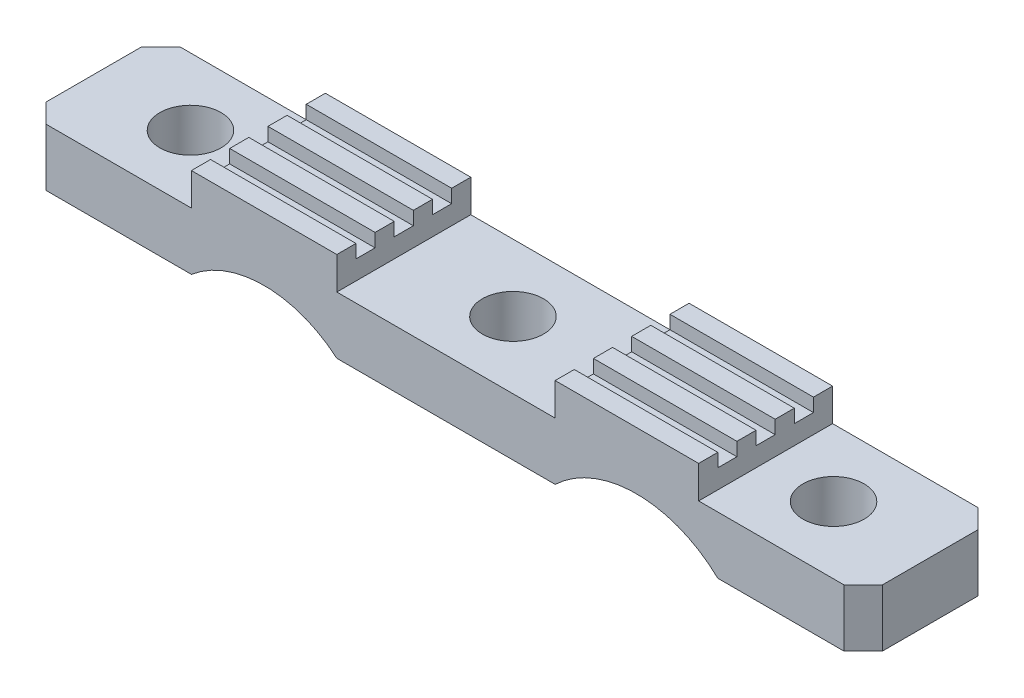
SolidWorks part; units mm, degrees
ref_plane "Front Plane" through (0, 0, 0) normal (0, 0, 1) x (1, 0, 0)
ref_plane "Top Plane" through (0, 0, 0) normal (0, 1, 0) x (1, 0, 0)
ref_plane "Right Plane" through (0, 0, 0) normal (1, 0, 0) x (0, 0, -1)
sketch "Sketch1" plane through (0, 0, 0) normal (0, 0, 1) x (1, 0, 0)
  line L0 (17.11, -3) -> (8.41, -3)
  line L1 (8.41, -3) -> (8.41, -5)
  line L2 (8.41, -5) -> (-2.8, -5)
  line L3 (-11.6, -5) -> (-11.5, -5)
  line L4 (17.11, -3) -> (17.11, -5)
  line L5 (17.11, -5) -> (22.11, -5)
  line L7 (-2.8, -5) -> (-2.8, -3)
  line L8 (-2.8, -3) -> (-11.6, -3)
  line L9 (-11.6, -3) -> (-11.6, -5)
  line L10 (-11.6, -5) -> (-16.6, -5)
  line L12 (-16.6, -5) -> (-16.6, -8)
  line L13 (-16.6, -8) -> (22.11, -8)
  line L14 (22.11, -8) -> (22.11, -5)
  line L15 (-11.5, -5) -> (-11.5, -3)
  line L16 (-2.8, -5) -> (-2.9, -5)
  line L17 (-2.9, -5) -> (-2.9, -3)
  line L18 (8.41, -5) -> (8.51, -5)
  line L19 (8.51, -5) -> (8.51, -3)
  line L20 (17.11, -5) -> (17.01, -5)
  line L21 (17.01, -5) -> (17.01, -3)
  point P7 (-16.6, -9.4349)
  dimension "D1" = 3
  dimension "D2" = 5
  dimension "D3" = 5
  dimension "D4" = 0.1
  dimension "D5" = 0.1
  dimension "D6" = 0.1
  dimension "D7" = 0.1
  dimension "D8" = 38.71
  dimension "D9" = 3
  dimension "D10" = 2
  dimension "D11" = 2
extrude "Boss-Extrude1" add sketch "Sketch1" against normal blind 7
sketch "Sketch2" plane through (-11.5, 0, 0) normal (-1, 0, 0) x (0, 0, 1)
  line L16 (0, -3) -> (-1, -3)
  line L17 (-7, -3) -> (0, -3) construction
  line L18 (-1, -3) -> (-1, -4)
  line L19 (-1, -4) -> (-2, -4)
  line L20 (-2, -4) -> (-2, -3)
  line L21 (-2, -3) -> (-3, -3)
  line L22 (-3, -3) -> (-3, -4)
  line L23 (-3, -4) -> (-4, -4)
  line L24 (-4, -4) -> (-4, -3)
  line L25 (-4, -3) -> (-5, -3)
  line L26 (-5, -3) -> (-5, -4)
  line L27 (-5, -4) -> (-6, -4)
  line L28 (-6, -4) -> (-6, -3)
  line L29 (-6, -3) -> (-7, -3)
  line L30 (-7, -3) -> (-7, -2.6458)
  line L31 (-7, -2.6458) -> (0, -2.6458)
  line L32 (0, -2.6458) -> (0, -3)
  dimension "D1" = 1
extrude "Cut-Extrude1" cut sketch "Sketch2" against normal up to surface (28.51 mm away) up to face at (17.01, -4, -3.5)
sketch "Sketch4" plane through (0, -5, 0) normal (0, 1, 0) x (1, 0, 0)
  line L0 (-2.9, 0) -> (8.51, 7) construction
  circle A0 centre (2.805, 3.5) radius 1.6
  dimension "D1" = 3.2
extrude "Cut-Extrude2" cut sketch "Sketch4" against normal up to surface (3 mm away) up to face at (2.755, -8, -3.5)
sketch "Sketch5" plane through (0, -5, 0) normal (0, 1, 0) x (1, 0, 0)
  line L0 (-16.6, 0) -> (-11.5, 7) construction
  line L1 (17.01, 0) -> (22.11, 7) construction
  circle A0 centre (-14.05, 3.5) radius 1.6
  circle A1 centre (19.56, 3.5) radius 1.6
  dimension "D1" = 3.2
  dimension "D2" = 3.2
extrude "Cut-Extrude3" cut sketch "Sketch5" against normal up to surface (3 mm away) up to face at (2.805, -8, -5.1)
sketch "Sketch6" plane through (17.01, 0, 0) normal (1, 0, 0) x (0, 0, -1)
  line L0 (7, -5) -> (7, -3) construction
  line L1 (0, -3) -> (7, -3)
  line L2 (0, -3) -> (0, -3.3)
  line L3 (0, -3.3) -> (7, -3.3)
  line L4 (7, -3) -> (7, -3.3)
  dimension "D1" = 0.3
extrude "Cut-Extrude4" cut sketch "Sketch6" against normal up to surface (28.51 mm away) up to face at (-11.5, -3.625, -3.5)
sketch "Sketch7" plane through (0, 0, 0) normal (0, 0, 1) x (1, 0, 0)
  line L0 (-16.6, -8) -> (22.11, -8) construction
  line L1 (-10.2, -7) -> (-4.2, -7)
  line L2 (-10.2, -7) -> (-10.2, -8)
  line L3 (-10.2, -8) -> (-4.2, -8)
  line L4 (-4.2, -7) -> (-4.2, -8)
  line L5 (9.76, -7) -> (15.76, -7)
  line L6 (9.76, -7) -> (9.76, -8)
  line L7 (9.76, -8) -> (15.76, -8)
  line L8 (15.76, -7) -> (15.76, -8)
  line L9 (-7.2, -7) -> (-7.2, -3.3) construction
  line L10 (-11.5, -3.3) -> (-2.9, -3.3) construction
  line L11 (12.76, -7) -> (12.76, -3.3) construction
  line L12 (8.51, -3.3) -> (17.01, -3.3) construction
  dimension "D1" = 6
  dimension "D2" = 6
  dimension "D3" = 1
sketch "Sketch8" plane through (-11.5, 0, 0) normal (-1, 0, 0) x (0, 0, 1)
  line L1 (-7, -5) -> (0, -5)
  line L2 (-7, -5) -> (-7, -3.3)
  line L3 (-7, -3.3) -> (0, -3.3)
  line L4 (0, -5) -> (0, -3.3)
extrude "Cut-Extrude6" cut sketch "Sketch8" against normal blind 1
sketch "Sketch9" plane through (0, -8, 0) normal (0, -1, 0) x (1, 0, 0)
  line L1 (-16.6, 0) -> (-19.1, 0)
  line L2 (-16.6, 0) -> (-16.6, -7)
  line L3 (-16.6, -7) -> (-19.1, -7)
  line L4 (-19.1, 0) -> (-19.1, -7)
  line L5 (22.11, 0) -> (24.61, 0)
  line L6 (22.11, 0) -> (22.11, -7)
  line L7 (22.11, -7) -> (24.61, -7)
  line L8 (24.61, 0) -> (24.61, -7)
  point P10 (22.11, -7)
  point P12 (-16.6, -7)
  dimension "D1" = 2.5
extrude "Boss-Extrude2" add sketch "Sketch9" against normal up to surface (3 mm away) up to face at (-14.05, -5, -1.9)
sketch "Sketch10" plane through (0, 0, -7) normal (0, 0, -1) x (-1, 0, 0)
  line L2 (19.1, -8) -> (-24.61, -8) construction
  line L3 (-17.01, -5) -> (-17.01, -8) construction
  line L4 (-8.51, -8) -> (-8.51, -5) construction
  line L5 (2.9, -5) -> (2.9, -8) construction
  line L6 (10.5, -5) -> (10.5, -8) construction
  line L7 (-12.76, -12.4625) -> (6.7, -12.4625) construction
  line L8 (-12.76, -6.3) -> (-12.76, -3.3) construction
  line L9 (-17.01, -8) -> (-8.51, -8)
  line L10 (2.9, -8) -> (10.5, -8)
  arc A2 (-17.01, -8) -> (-8.51, -8) centre (-12.76, -12.4625) cw
  arc A3 (2.9, -8) -> (10.5, -8) centre (6.7, -12.4625) cw
  dimension "D1" = 3
extrude "Cut-Extrude7" cut sketch "Sketch10" against normal up to surface (7 mm away) up to face at (2.9383, -4.9333, 0)
chamfer "Chamfer1" distance 1 angle 45 4 edges at (24.61, -6.5, 0) (24.61, -6.5, -7) (-19.1, -6.5, -7) (-19.1, -6.5, 0)
sketch "Sketch11" plane through (17.01, 0, 0) normal (1, 0, 0) x (0, 0, -1)
  line L1 (0, -5) -> (7, -5)
  line L2 (0, -5) -> (0, -3.3)
  line L3 (0, -3.3) -> (7, -3.3)
  line L4 (7, -5) -> (7, -3.3)
extrude "Cut-Extrude8" cut sketch "Sketch11" against normal blind 1
